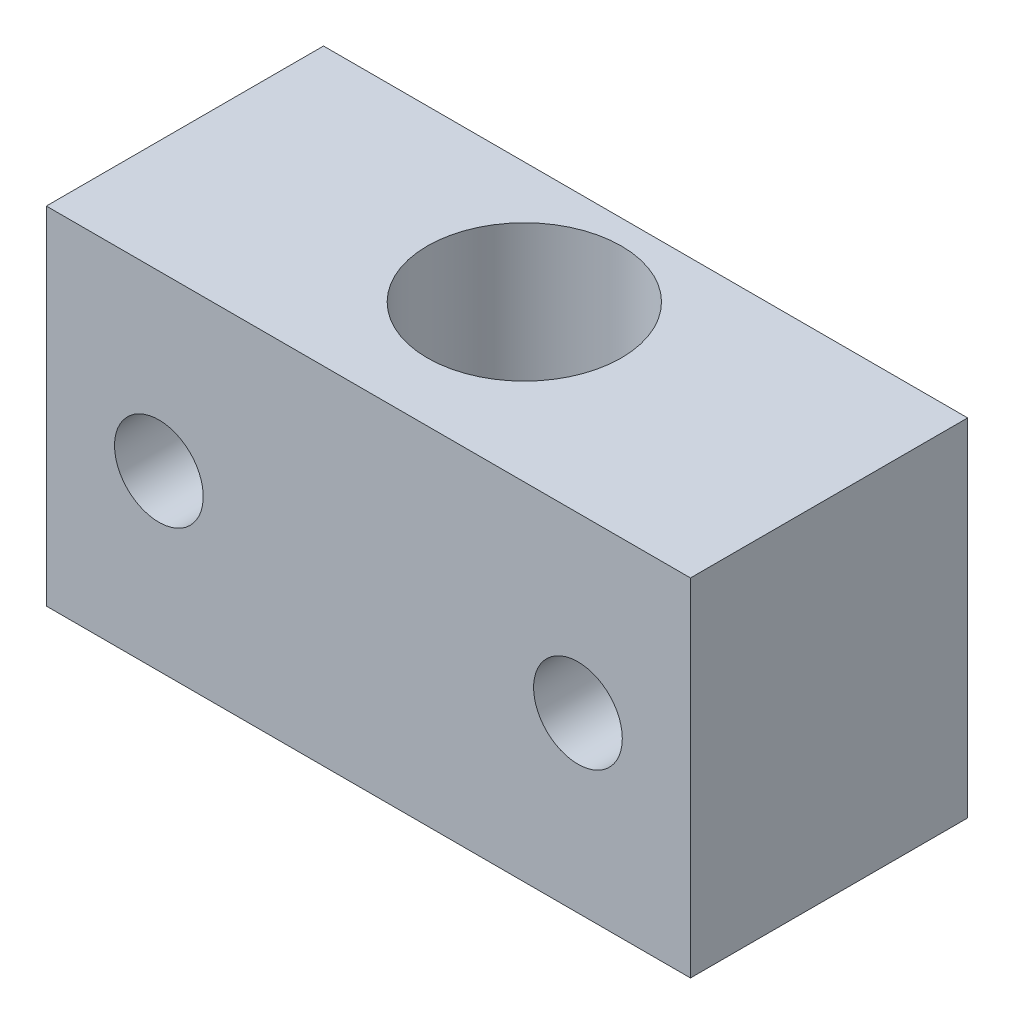
SolidWorks part; units mm, degrees
material "Polyethylene Cross-Linked"
ref_plane "Front Plane" through (0, 0, 0) normal (0, 0, 1) x (1, 0, 0)
ref_plane "Top Plane" through (0, 0, 0) normal (0, 1, 0) x (1, 0, 0)
ref_plane "Right Plane" through (0, 0, 0) normal (1, 0, 0) x (0, 0, -1)
sketch "Sketch1" plane through (0, 0, 0) normal (0, 1, 0) x (1, 0, 0)
  line L1 (0, 0) -> (29.5139, 0)
  line L2 (0, 0) -> (0, 12.7)
  line L3 (0, 12.7) -> (29.5139, 12.7)
  line L4 (29.5139, 0) -> (29.5139, 12.7)
  circle A0 centre (14.7569, 7.1438) radius 4.445
extrude "Boss-Extrude1" add sketch "Sketch1" along normal blind 15.875
sketch "Sketch2" plane through (0, 0, -12.7) normal (0, 0, -1) x (-1, 0, 0)
  circle A0 centre (-5.156, 7.9375) radius 2.032
  circle A1 centre (-24.3579, 7.9375) radius 2.032
  point P9 (-14.7569, 7.9375)
extrude "Cut-Extrude1" cut sketch "Sketch2" against normal blind 12.7
